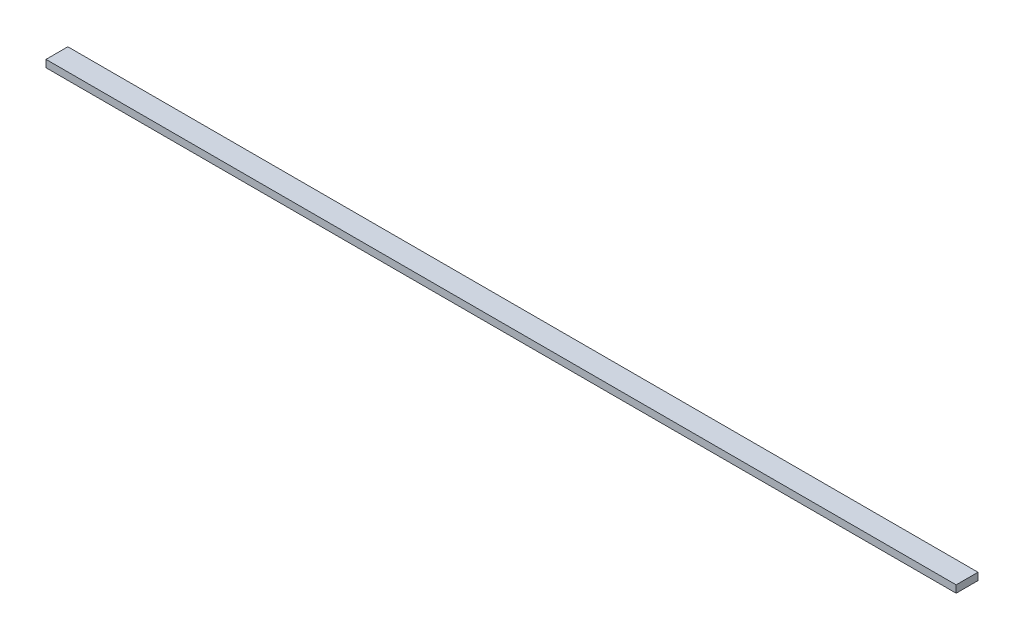
SolidWorks part; units mm, degrees
ref_plane "Front Plane" through (0, 0, 0) normal (0, 0, 1) x (1, 0, 0)
ref_plane "Top Plane" through (0, 0, 0) normal (0, 1, 0) x (1, 0, 0)
ref_plane "Right Plane" through (0, 0, 0) normal (1, 0, 0) x (0, 0, -1)
sketch "Sketch1" plane through (0, 0, 0) normal (0, 1, 0) x (1, 0, 0)
  line L0 (-625, 15) -> (625, -15) construction
  line L1 (-625, 15) -> (625, 15)
  line L2 (-625, 15) -> (-625, -15)
  line L3 (-625, -15) -> (625, -15)
  line L4 (625, 15) -> (625, -15)
  dimension "D1" = 1250
  dimension "D2" = 30
extrude "Boss-Extrude1" add sketch "Sketch1" along normal blind 10
